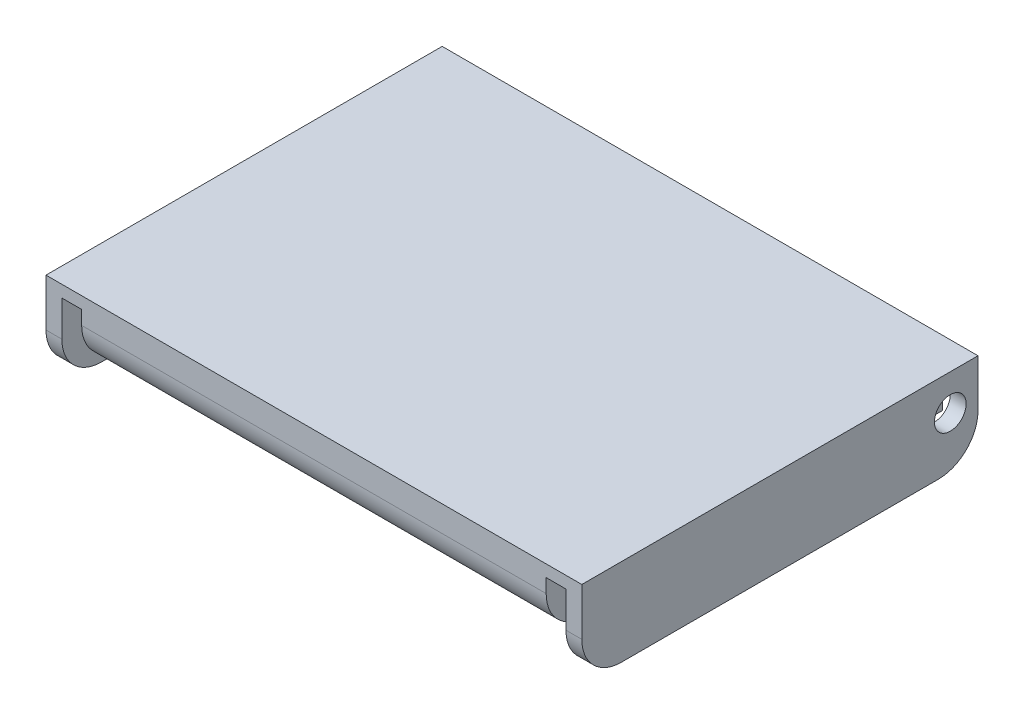
SolidWorks part; units mm, degrees
ref_plane "Front Plane" through (0, 0, 0) normal (0, 0, 1) x (1, 0, 0)
ref_plane "Top Plane" through (0, 0, 0) normal (0, 1, 0) x (1, 0, 0)
ref_plane "Right Plane" through (0, 0, 0) normal (1, 0, 0) x (0, 0, -1)
sketch "Sketch1" plane through (0, 0, 0) normal (0, 1, 0) x (1, 0, 0)
  line L1 (67.625, 50) -> (-67.625, 50)
  line L2 (67.625, 50) -> (67.625, -50)
  line L3 (67.625, -50) -> (-67.625, -50)
  line L4 (-67.625, 50) -> (-67.625, -50)
  line L5 (67.625, 50) -> (-67.625, -50) construction
  line L6 (67.625, -50) -> (-67.625, 50) construction
  point P0 (0, 0)
  dimension "D1" = 135.25
  dimension "D2" = 100
extrude "Boss-Extrude1" add sketch "Sketch1" along normal blind 22
sketch "Sketch4" plane through (0, 0, 50) normal (0, 0, 1) x (1, 0, 0)
  line L0 (-67.625, 0) -> (67.625, 0) construction
  line L1 (-63.625, 19) -> (-58.625, 19)
  line L2 (-63.625, 19) -> (-63.625, 0)
  line L3 (-63.625, 0) -> (-58.625, 0)
  line L4 (-58.625, 19) -> (-58.625, 0)
  line L5 (-63.625, 19) -> (-58.625, 0) construction
  line L6 (-63.625, 0) -> (-58.625, 19) construction
  line L7 (-67.625, 22) -> (-67.625, 0) construction
  line L8 (0, 0) -> (0, 39.0238) construction
  line L9 (63.625, 0) -> (58.625, 0)
  line L10 (58.625, 19) -> (58.625, 0)
  line L11 (63.625, 19) -> (58.625, 19)
  line L12 (63.625, 19) -> (63.625, 0)
  point P0 (-61.125, 9.5)
  dimension "D1" = 5
  dimension "D2" = 4
  dimension "D3" = 19
extrude "Cut-Extrude1" cut sketch "Sketch4" against normal through all
sketch "Sketch5" plane through (0, 0, -50) normal (0, 0, -1) x (-1, 0, 0)
  line L0 (-58.625, 19) -> (-58.625, 0) construction
  line L1 (58.625, -5.5) -> (-58.625, -5.5)
  line L2 (58.625, -5.5) -> (58.625, 5.5)
  line L3 (58.625, 5.5) -> (-58.625, 5.5)
  line L4 (-58.625, -5.5) -> (-58.625, 5.5)
  line L5 (58.625, -5.5) -> (-58.625, 5.5) construction
  line L6 (58.625, 5.5) -> (-58.625, -5.5) construction
  point P0 (0, 0)
  dimension "D1" = 11
extrude "Cut-Extrude2" cut sketch "Sketch5" against normal through all
fillet "Fillet1" radius 10 1 edges at (0, 5.5, 50)
fillet "Fillet2" radius 10 1 edges at (-65.625, 0, 50)
fillet "Fillet3" radius 10 1 edges at (65.625, 0, 50)
fillet "Fillet4" radius 10 1 edges at (-65.625, 0, -50)
fillet "Fillet5" radius 10 1 edges at (65.625, 0, -50)
sketch "Sketch6" plane through (-67.625, 0, 0) normal (-1, 0, 0) x (0, 0, 1)
  line L0 (-50, 22) -> (-50, 10) construction
  line L1 (-50, 22) -> (50, 22) construction
  circle A0 centre (-43, 13) radius 4
  dimension "D1" = 8
  dimension "D2" = 7
  dimension "D3" = 9
extrude "Cut-Extrude3" cut sketch "Sketch6" against normal through all
